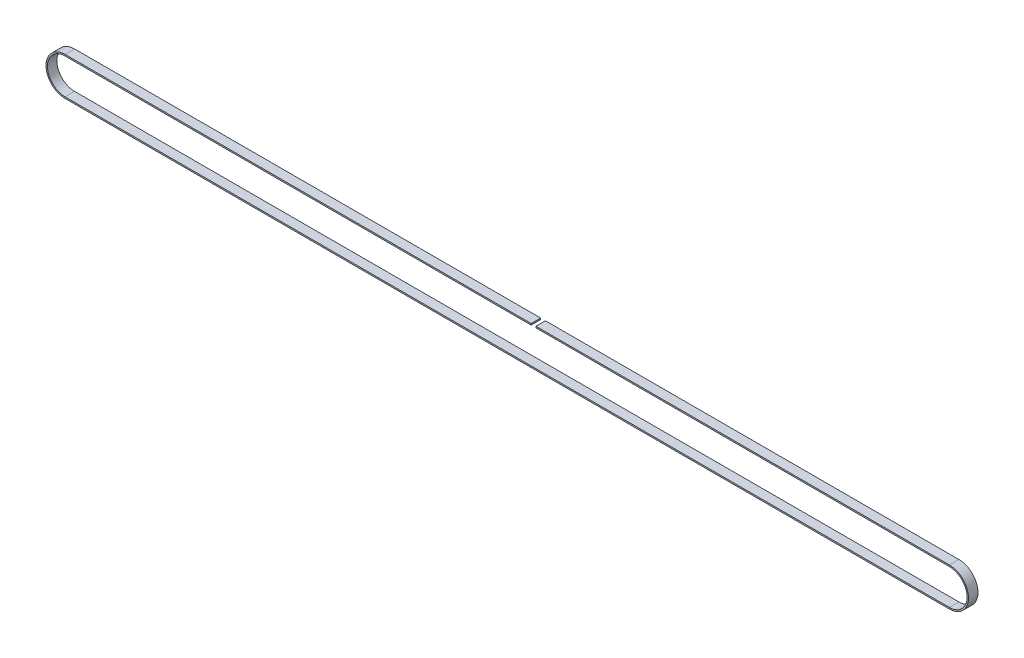
SolidWorks part; units mm, degrees
ref_plane "前基準面" through (0, 0, 0) normal (0, 0, 1) x (1, 0, 0)
ref_plane "上基準面" through (0, 0, 0) normal (0, 1, 0) x (1, 0, 0)
ref_plane "右基準面" through (0, 0, 0) normal (1, 0, 0) x (0, 0, -1)
sketch "草圖1" plane through (0, 0, 0) normal (0, 0, 1) x (1, 0, 0)
  line L0 (-466, 0) -> (466, 0) construction
  line L1 (-466, 18.62) -> (466, 18.62)
  line L2 (-466, -18.62) -> (466, -18.62)
  line L3 (-466, 18.62) -> (-466, 0) construction
  line L4 (-466, 0) -> (-466, -18.62) construction
  line L5 (466, 18.62) -> (466, 0) construction
  line L6 (466, 0) -> (466, -18.62) construction
  line L7 (-466, 20.12) -> (466, 20.12)
  line L8 (-466, -20.12) -> (466, -20.12)
  arc A0 (466, -18.62) -> (466, 18.62) centre (466, 0) ccw
  arc A1 (-466, 18.62) -> (-466, -18.62) centre (-466, 0) ccw
  arc A2 (466, -20.12) -> (466, 20.12) centre (466, 0) ccw
  arc A3 (-466, 20.12) -> (-466, -20.12) centre (-466, 0) ccw
  dimension "D2" = 37.24
  dimension "D3" = 37.24
  dimension "D1" = 932
  dimension "D4" = 180
  dimension "D5" = 180
  dimension "D6" = 932
  dimension "D7" = 932
  dimension "D8" = 1.5
extrude "伸長1" add sketch "草圖1" along normal blind 10
sketch "草圖2" plane through (0, 20.12, 0) normal (0, 1, 0) x (1, 0, 0)
  line L1 (25.1777, -10) -> (30.1777, -10)
  line L2 (25.1777, -10) -> (25.1777, 0)
  line L3 (25.1777, 0) -> (30.1777, 0)
  line L4 (30.1777, -10) -> (30.1777, 0)
  line L5 (466, -10) -> (-466, -10) construction
  line L6 (466, 0) -> (-466, 0) construction
  dimension "D1" = 5
extrude "除料-伸長1" cut sketch "草圖2" against normal up to next
